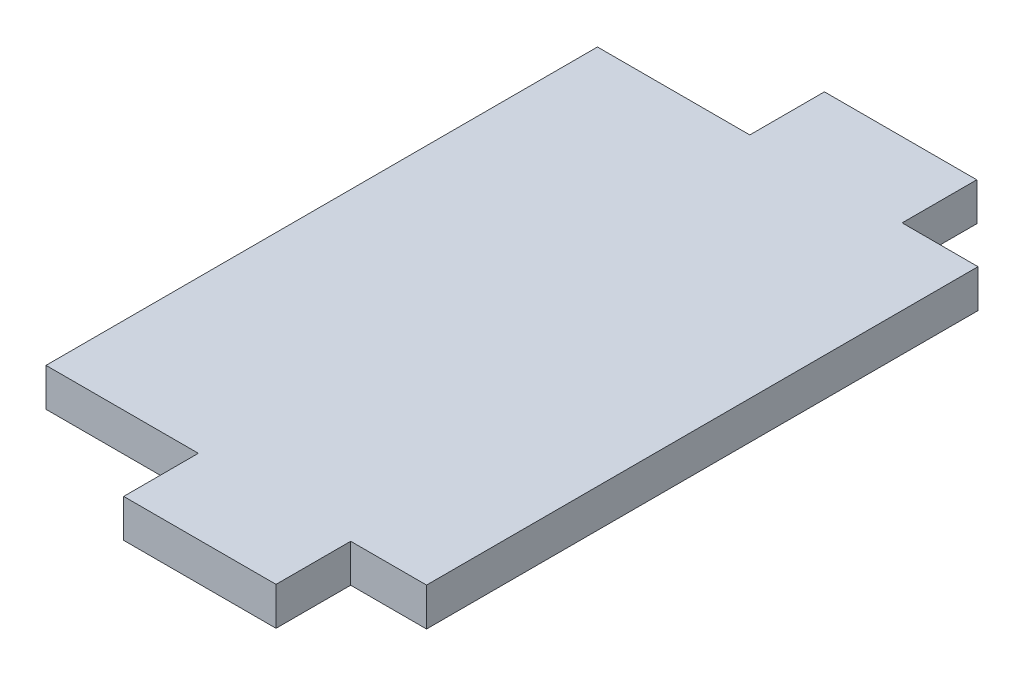
SolidWorks part; units mm, degrees
ref_plane "Front Plane" through (0, 0, 0) normal (0, 0, 1) x (1, 0, 0)
ref_plane "Top Plane" through (0, 0, 0) normal (0, 1, 0) x (1, 0, 0)
ref_plane "Right Plane" through (0, 0, 0) normal (1, 0, 0) x (0, 0, -1)
sketch "Sketch1" plane through (0, 0, 0) normal (0, 1, 0) x (1, 0, 0)
  line L0 (-12.7, 29.21) -> (-25.4, 29.21) construction
  line L1 (0, 0) -> (-12.7, 0)
  line L2 (0, 0) -> (0, 6.223)
  line L3 (0, 58.42) -> (-12.7, 58.42)
  line L4 (-12.7, 0) -> (-12.7, 6.223)
  line L5 (0, 52.197) -> (6.3246, 52.197)
  line L6 (-12.7, 52.197) -> (-12.7, 58.42)
  line L7 (0, 6.223) -> (6.3246, 6.223)
  line L8 (6.3246, 52.197) -> (6.3246, 6.223)
  line L9 (-12.7, 6.223) -> (-25.4, 6.223)
  line L11 (-12.7, 52.197) -> (-25.4, 52.197)
  line L12 (-25.4, 6.223) -> (-25.4, 52.197)
  line L13 (0, 29.21) -> (-12.7, 29.21) construction
  line L14 (6.3246, 29.21) -> (0, 29.21) construction
  line L15 (0, 52.197) -> (0, 58.42)
  dimension "D1" = 12.7
  dimension "D2" = 6.3246
  dimension "D3" = 12.7
  dimension "D4" = 45.974
  dimension "D5" = 58.42
  dimension "D6" = 45.974
extrude "Boss-Extrude1" add sketch "Sketch1" along normal blind 3.175
